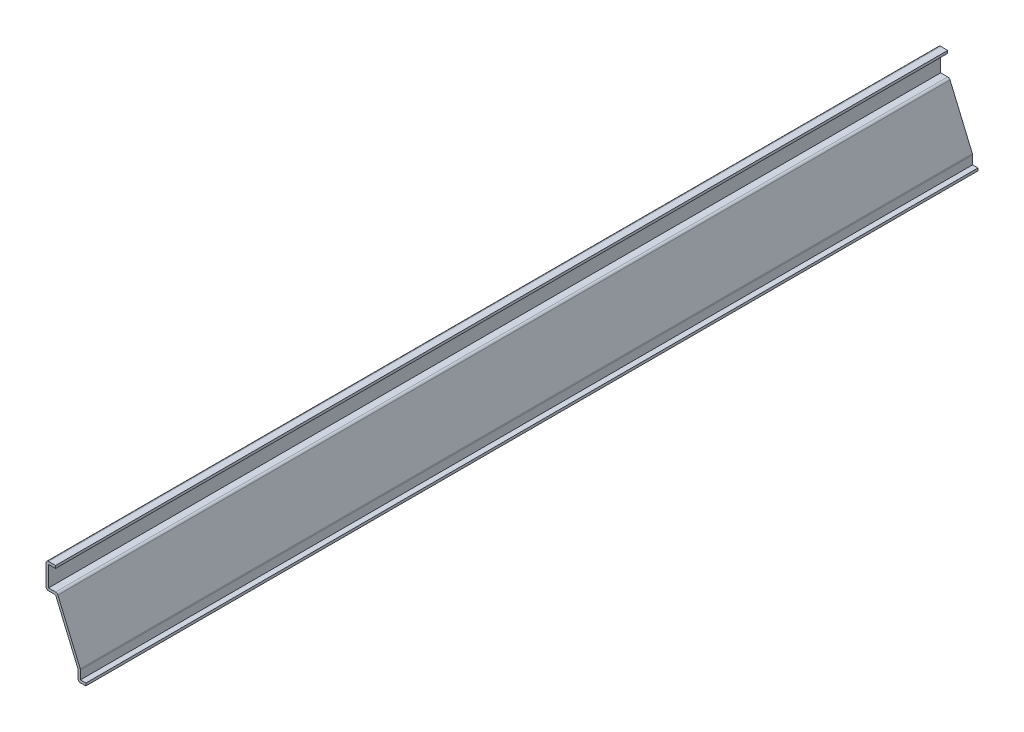
SolidWorks part; units mm, degrees
ref_plane "Front Plane" through (0, 0, 0) normal (0, 0, 1) x (1, 0, 0)
ref_plane "Top Plane" through (0, 0, 0) normal (0, 1, 0) x (1, 0, 0)
ref_plane "Right Plane" through (0, 0, 0) normal (1, 0, 0) x (0, 0, -1)
sketch "Sketch1" plane through (0, 0, 0) normal (0, 0, 1) x (1, 0, 0)
  line L0 (0, 0) -> (-3.9688, 0)
  line L1 (-3.9688, 0) -> (-3.9688, 5.5562)
  line L2 (-3.9688, 5.5562) -> (-15.0813, 31.75)
  line L3 (-15.0813, 31.75) -> (-19.8438, 31.75)
  line L4 (-19.8438, 31.75) -> (-19.8438, 44.45)
  line L5 (-19.8438, 44.45) -> (-15.0813, 44.45)
  point P3 (-11.9824, 31.75)
  point P9 (0, 0)
  dimension "D1" = 3.9688
  dimension "D2" = 19.8438
  dimension "D3" = 15.875
  dimension "D4" = 5.5562
  dimension "D5" = 26.1937
  dimension "D6" = 12.7
  dimension "D7" = 4.7625
  dimension "D8" = 44.45
extrude "Extrude-Thin1" add sketch "Sketch1" against normal blind 444.5 thin
fillet "Fillet1" radius 1.27 5 edges at (-3.9688, 0, -222.25) (-2.6987, 5.8145, -222.25) (-14.2405, 33.02, -222.25) (-19.8438, 31.75, -222.25) (-19.8438, 44.45, -222.25)
